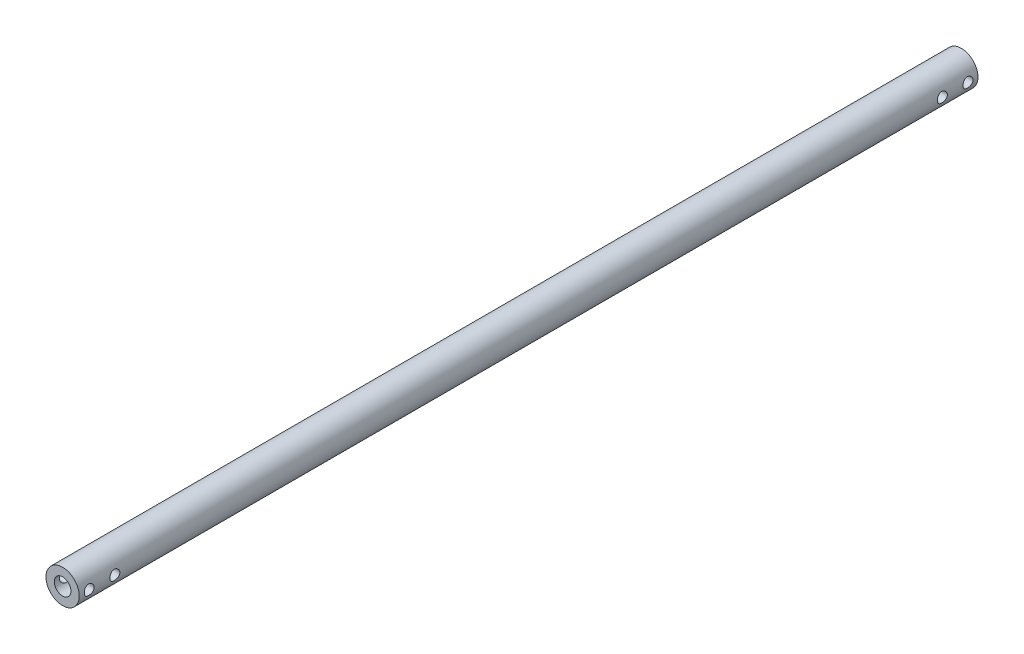
SolidWorks part; units mm, degrees
material "6061-T6 (SS)"
ref_plane "Front Plane" through (0, 0, 0) normal (0, 0, 1) x (1, 0, 0)
ref_plane "Top Plane" through (0, 0, 0) normal (0, 1, 0) x (1, 0, 0)
ref_plane "Right Plane" through (0, 0, 0) normal (1, 0, 0) x (0, 0, -1)
sketch "Sketch2" plane through (0, 0, 0) normal (0, 0, 1) x (1, 0, 0)
  circle A0 centre (0, 0) radius 6.35
  dimension "D1" = 12.7
extrude "Boss-Extrude1" add sketch "Sketch2" along normal blind 342.9
sketch "Sketch3" plane through (0, 0, 0) normal (1, 0, 0) x (0, 0, -1)
  line L1 (0, -6.35) -> (0, 6.35) construction
  line L5 (-171.45, -27.1311) -> (-171.45, 0) construction
  line L6 (0, 0) -> (-342.9, 0) construction
  line L7 (-342.9, 6.35) -> (-342.9, -6.35) construction
  circle A0 centre (-339.09, 0) radius 1.905
  circle A1 centre (-329.311, 0) radius 1.905
  circle A2 centre (-13.589, 0) radius 1.905
  circle A3 centre (-3.81, 0) radius 1.905
  dimension "D4" = 3.81
  dimension "D5" = 9.779
extrude "Cut-Extrude5" cut sketch "Sketch3" against normal mid plane 355.6
ref_plane "Plane1" through (0, 0, 171.45) normal (0, 0, 1) x (1, 0, 0)
sketch "Sketch4" plane through (0, 0, 0) normal (0, 0, -1) x (-1, 0, 0)
  circle A0 centre (0, 0) radius 3.175
  dimension "D1" = 6.35
extrude "Cut-Extrude6" cut sketch "Sketch4" against normal through all
